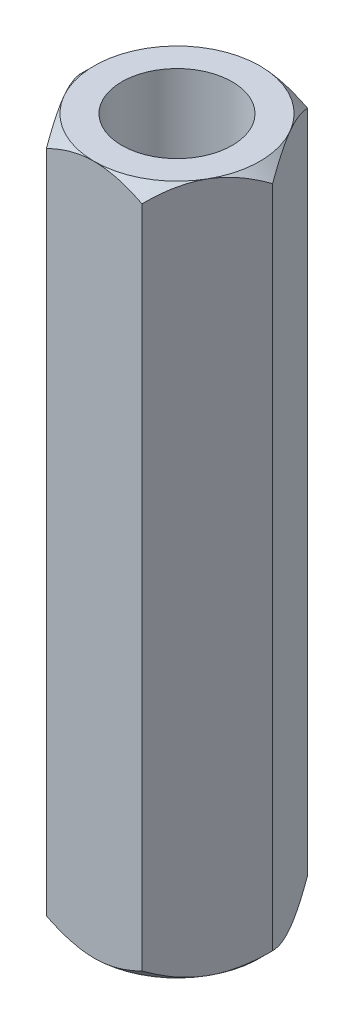
SolidWorks part; units mm, degrees
ref_plane "前视基准面" through (0, 0, 0) normal (0, 0, 1) x (1, 0, 0)
ref_plane "上视基准面" through (0, 0, 0) normal (0, 1, 0) x (1, 0, 0)
ref_plane "右视基准面" through (0, 0, 0) normal (1, 0, 0) x (0, 0, -1)
sketch "草图1" plane through (0, 0, 0) normal (0, 1, 0) x (1, 0, 0)
  circle A0 centre (0, 0) radius 3.5
  circle A1 centre (0, 0) radius 2
  dimension "D1" = 4
  dimension "D2" = 7
extrude "凸台-拉伸1" add sketch "草图1" along normal blind 25
chamfer "倒角1" distance 0.5 angle 45 2 edges at (0, 0, 3.5) (0, 25, 3.5)
sketch "草图2" plane through (0, 25, 0) normal (0, 1, 0) x (1, 0, 0)
  line L1 (1.7321, 3) -> (-1.7321, 3)
  line L2 (-1.7321, 3) -> (-3.4641, 0)
  line L3 (-3.4641, 0) -> (-1.7321, -3)
  line L4 (-1.7321, -3) -> (1.7321, -3)
  line L5 (1.7321, -3) -> (3.4641, 0)
  line L6 (3.4641, 0) -> (1.7321, 3)
  circle A0 centre (0, 0) radius 3 construction
  dimension "D1" = 6
extrude "切除-拉伸1" cut sketch "草图2" against normal through all flip side to cut
